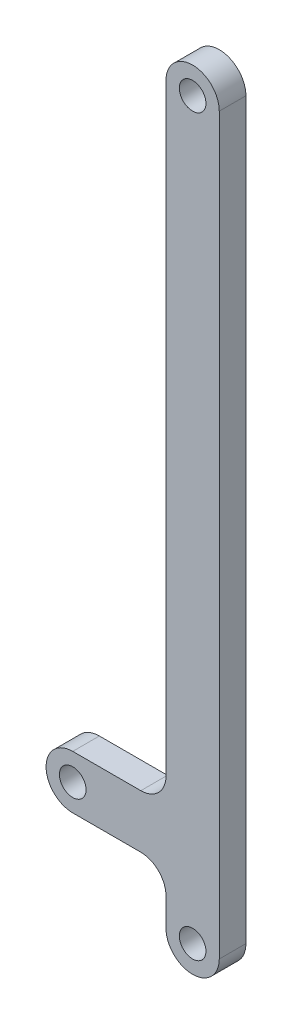
SolidWorks part; units mm, degrees
material "7075-T6, Plate (SS)"
ref_plane "Front Plane" through (0, 0, 0) normal (0, 0, 1) x (1, 0, 0)
ref_plane "Top Plane" through (0, 0, 0) normal (0, 1, 0) x (1, 0, 0)
ref_plane "Right Plane" through (0, 0, 0) normal (1, 0, 0) x (0, 0, -1)
sketch "Sketch1" plane through (0, 0, 0) normal (0, 0, 1) x (1, 0, 0)
  line L0 (-12.7, -336.612) -> (-12.7, -350)
  line L2 (-12.7, 0) -> (-12.7, -287.212)
  line L4 (12.7, 0) -> (12.7, -350)
  line L5 (-24.7, -299.212) -> (-57.15, -299.212)
  line L7 (-24.7, -324.612) -> (-57.15, -324.612)
  arc A0 (-12.7, 0) -> (12.7, 0) centre (0, 0) cw
  arc A1 (-12.7, -350) -> (12.7, -350) centre (0, -350) ccw
  arc A2 (-57.15, -299.212) -> (-57.15, -324.612) centre (-57.15, -311.912) ccw
  circle A3 centre (0, 0) radius 6.35
  circle A4 centre (-57.15, -311.912) radius 6.35
  circle A5 centre (0, -350) radius 6.35
  arc A6 (-12.7, -336.612) -> (-24.7, -324.612) centre (-24.7, -336.612) ccw
  arc A7 (-24.7, -299.212) -> (-12.7, -287.212) centre (-24.7, -287.212) ccw
  point P18 (-12.7, -299.212)
  dimension "D6" = 12.7
  dimension "D7" = 12
  dimension "D1" = 25.4
  dimension "D2" = 350
  dimension "D3" = 25.4
  dimension "D4" = 44.45
  dimension "D5" = 299.212
  dimension "D8" = 0
  dimension "D9" = 0
extrude "Boss-Extrude3" add sketch "Sketch1" along normal blind 12.7
